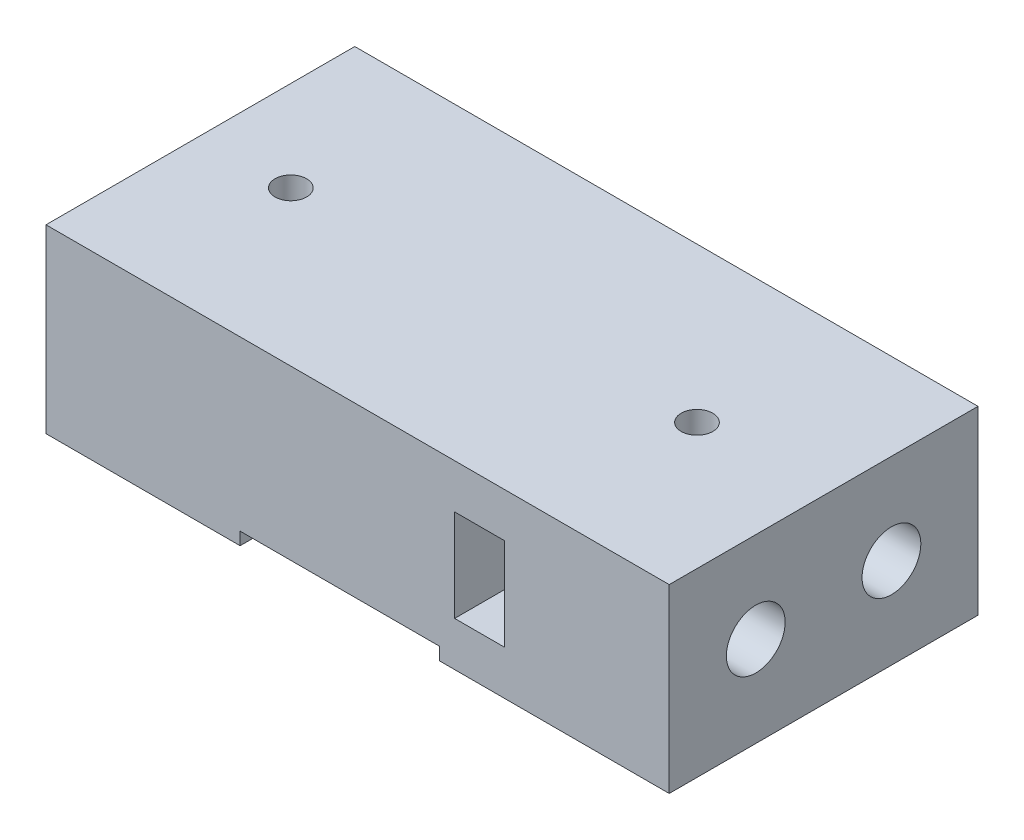
SolidWorks part; units mm, degrees
ref_plane "Front Plane" through (0, 0, 0) normal (0, 0, 1) x (1, 0, 0)
ref_plane "Top Plane" through (0, 0, 0) normal (0, 1, 0) x (1, 0, 0)
ref_plane "Right Plane" through (0, 0, 0) normal (1, 0, 0) x (0, 0, -1)
sketch "Sketch1" plane through (0, 0, 0) normal (0, 1, 0) x (1, 0, 0)
  line L1 (-34.448, 17.0677) -> (34.448, 17.0677)
  line L2 (-34.448, 17.0677) -> (-34.448, -17.0677)
  line L3 (-34.448, -17.0677) -> (34.448, -17.0677)
  line L4 (34.448, 17.0677) -> (34.448, -17.0677)
  line L5 (-34.448, 17.0677) -> (34.448, -17.0677) construction
  line L6 (-34.448, -17.0677) -> (34.448, 17.0677) construction
  point P0 (0, 0)
extrude "Boss-Extrude1" add sketch "Sketch1" along normal blind 20
sketch "Sketch2" plane through (0, 0, -17.0677) normal (0, 0, -1) x (-1, 0, 0)
  line L0 (-34.448, 0) -> (34.448, 0) construction
  line L1 (12.9895, 0) -> (-9.0428, 0)
  line L2 (12.9895, 0) -> (12.9895, 1.4)
  line L3 (12.9895, 1.4) -> (-9.0428, 1.4)
  line L4 (-9.0428, 0) -> (-9.0428, 1.4)
  dimension "D1" = 1.4
extrude "Cut-Extrude1" cut sketch "Sketch2" against normal up to next
sketch "Sketch7" plane through (34.448, 0, 0) normal (1, 0, 0) x (0, 0, -1)
  line L0 (0, 0) -> (0, 20) construction
  line L2 (-7.5, 10) -> (7.5, 10) construction
  line L3 (-17.0677, 0) -> (17.0677, 0) construction
  line L4 (-17.0677, 20) -> (17.0677, 20) construction
  circle A0 centre (-7.5, 10) radius 3.25
  circle A1 centre (7.5, 10) radius 3.25
  point P10 (0, 10)
  dimension "D1" = 6.5
  dimension "D2" = 6.5
  dimension "D3" = 15
extrude "Cut-Extrude4" cut sketch "Sketch7" against normal blind 30
sketch "Sketch8" plane through (0, 0, 0) normal (0, -1, 0) x (1, 0, 0)
  circle A0 centre (-24.448, 0) radius 1.75
  circle A1 centre (20.448, 0) radius 1.75
  dimension "D1" = 3.5
extrude "Cut-Extrude5" cut sketch "Sketch8" against normal up to next
sketch "Sketch9" plane through (0, 0, -17.0677) normal (0, 0, -1) x (-1, 0, 0)
  line L0 (-34.448, 10) -> (47.2849, 10) construction
  line L1 (-16.2259, 15.1) -> (-10.7259, 15.1)
  line L2 (-16.2259, 15.1) -> (-16.2259, 4.9)
  line L3 (-16.2259, 4.9) -> (-10.7259, 4.9)
  line L4 (-10.7259, 15.1) -> (-10.7259, 4.9)
  line L5 (-34.448, 20) -> (-34.448, 0) construction
  point P8 (-10.7259, 10)
  dimension "D1" = 10.2
  dimension "D2" = 5.5
extrude "Cut-Extrude6" cut sketch "Sketch9" against normal through all
sketch "Sketch10" plane through (0, 1.4, 0) normal (0, -1, 0) x (1, 0, 0)
  line L0 (9.0428, 17.0677) -> (9.0428, -17.0677) construction
  line L1 (9.0428, 15.155) -> (-12.9895, 15.155)
  line L2 (9.0428, 15.155) -> (9.0428, 12.355)
  line L3 (9.0428, 12.355) -> (-12.9895, 12.355)
  line L4 (-12.9895, 15.155) -> (-12.9895, 12.355)
  line L5 (-12.9895, 17.0677) -> (-12.9895, -17.0677) construction
  dimension "D1" = 2.8
extrude "Cut-Extrude7" cut sketch "Sketch10" against normal blind 1.5 draft 20
pattern_linear "LPattern1" count 7 spacing 5 along (0, 0, -1) of "Cut-Extrude7"
